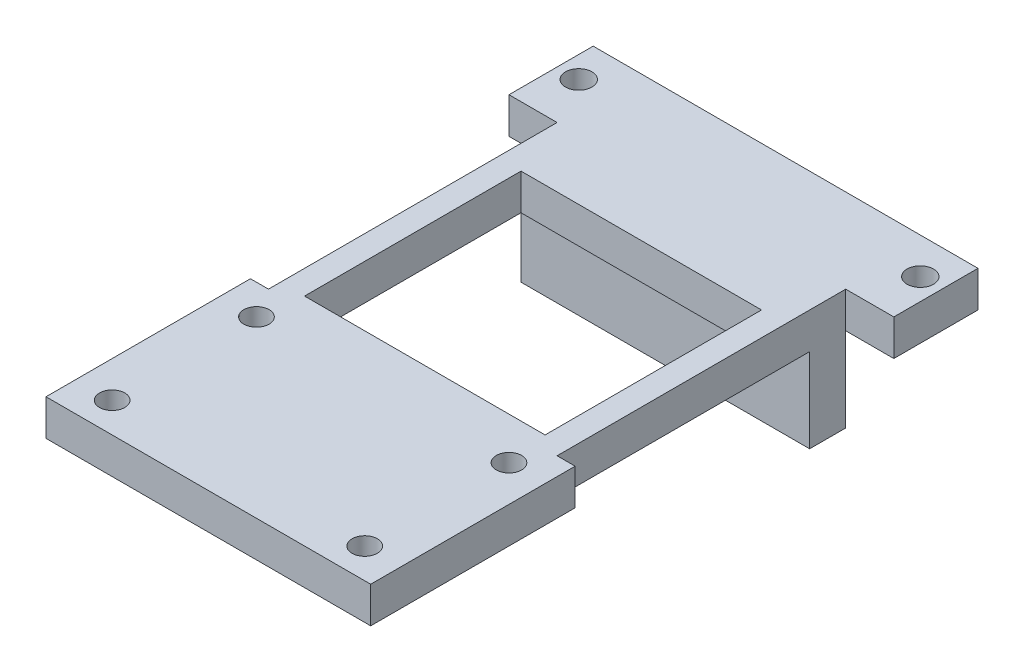
SolidWorks part; units mm, degrees
ref_plane "前视基准面" through (0, 0, 0) normal (0, 0, 1) x (1, 0, 0)
ref_plane "上视基准面" through (0, 0, 0) normal (0, 1, 0) x (1, 0, 0)
ref_plane "右视基准面" through (0, 0, 0) normal (1, 0, 0) x (0, 0, -1)
sketch "草图1" plane through (0, 0, 0) normal (0, 0, 1) x (1, 0, 0)
  line L1 (0, 0) -> (20, 0)
  line L2 (0, 0) -> (0, 10)
  line L3 (0, 10) -> (20, 10)
  line L4 (20, 0) -> (20, 10)
  dimension "D1" = 10
  dimension "D2" = 20
extrude "凸台-拉伸1" add sketch "草图1" along normal blind 3
sketch "草图2" plane through (0, 0, 3) normal (0, 0, 1) x (1, 0, 0)
  line L0 (20, 0) -> (20, 10) construction
  line L1 (0, 10) -> (20, 10)
  line L2 (0, 10) -> (0, 7)
  line L3 (0, 7) -> (20, 7)
  line L4 (20, 10) -> (20, 7)
  dimension "D1" = 3
extrude "凸台-拉伸2" add sketch "草图2" along normal blind 18
sketch "草图3" plane through (0, 7, 0) normal (0, -1, 0) x (1, 0, 0)
  line L0 (0, 3) -> (20, 3) construction
  line L1 (2, 18) -> (18, 18)
  line L2 (2, 18) -> (2, 6)
  line L3 (2, 6) -> (18, 6)
  line L4 (18, 18) -> (18, 6)
  line L6 (0, 21) -> (0, 3) construction
  line L7 (20, 21) -> (20, 3) construction
  dimension "D1" = 3
  dimension "D2" = 12
  dimension "D3" = 2
  dimension "D4" = 2
extrude "切除-拉伸1" cut sketch "草图3" against normal blind 8
sketch "草图4" plane through (0, 7, 0) normal (0, -1, 0) x (1, 0, 0)
  line L0 (0, 21) -> (-3.5, 21)
  line L1 (-3.5, 21) -> (-3.5, 38)
  line L2 (-3.5, 38) -> (23.5, 38)
  line L3 (23.5, 38) -> (23.5, 21)
  line L4 (23.5, 21) -> (0, 21)
  line L5 (0, 21) -> (0, 3) construction
  dimension "D1" = 27
  dimension "D2" = 3.5
  dimension "D3" = 17
extrude "凸台-拉伸3" add sketch "草图4" against normal blind 3
sketch "草图5" plane through (0, 7, 0) normal (0, -1, 0) x (1, 0, 0)
  line L0 (-3.5, 38) -> (-3.5, 21) construction
  line L1 (23.5, 21) -> (23.5, 38) construction
  line L2 (-3.5, 21) -> (0, 21) construction
  circle A0 centre (-0.5, 23.5) radius 1.05
  circle A1 centre (20.5, 23.5) radius 1.05
  circle A2 centre (20.5, 35.5) radius 1.05
  circle A3 centre (-0.5, 35.5) radius 1.05
  dimension "D1" = 2.1
  dimension "D2" = 2.1
  dimension "D3" = 2.1
  dimension "D4" = 2.1
  dimension "D5" = 21
  dimension "D6" = 3
  dimension "D7" = 3
  dimension "D8" = 21
  dimension "D9" = 3
  dimension "D10" = 3
  dimension "D11" = 12
  dimension "D12" = 2.5
extrude "切除-拉伸2" cut sketch "草图5" against normal blind 10
fillet "圆角2" radius 1 1 edges at (10, 0, 3)
fillet "圆角3" radius 1 6 edges at (20, 0, 1) (20, 0.2929, 2.7071) (0, 0, 1) (0, 0.2929, 2.7071) (20, 4, 3) (0, 4, 3)
fillet "圆角4" radius 1 4 edges at (10, 7, 6) (2, 7, 12) (18, 7, 12) (10, 7, 18)
sketch "草图6" plane through (0, 10, 0) normal (0, 1, 0) x (1, 0, 0)
  line L0 (0, -21) -> (0, 0)
  line L1 (0, 0) -> (20, 0)
  line L2 (20, 0) -> (20, -21)
  line L3 (20, -21) -> (0, -21)
extrude "切除-拉伸3" cut sketch "草图6" against normal blind 10
sketch "草图7" plane through (0, 10, 0) normal (0, 1, 0) x (1, 0, 0)
  line L0 (22, -21) -> (22, 3)
  line L1 (-3.5, -21) -> (23.5, -21) construction
  line L2 (22, 3) -> (-2, 3)
  line L3 (-2, 3) -> (-2, -21)
  line L4 (22, -21) -> (-2, -21)
  line L5 (23.5, -21) -> (23.5, -38) construction
  dimension "D1" = 24
  dimension "D2" = 1.5
  dimension "D3" = 24
extrude "凸台-拉伸4" add sketch "草图7" against normal blind 3
sketch "草图8" plane through (0, 7, 0) normal (0, -1, 0) x (1, 0, 0)
  line L0 (22, 21) -> (22, -3) construction
  line L1 (-2, -3) -> (22, -3)
  line L2 (-2, -3) -> (-2, 0)
  line L3 (-2, 0) -> (22, 0)
  line L4 (22, -3) -> (22, 0)
  dimension "D1" = 3
extrude "凸台-拉伸5" add sketch "草图8" along normal blind 7
sketch "草图9" plane through (0, 10, 0) normal (0, 1, 0) x (1, 0, 0)
  line L10 (22, 3) -> (-2, 3) construction
  line L11 (20, -20) -> (0, -20)
  line L12 (20, -20) -> (20, -2)
  line L13 (20, -2) -> (0, -2)
  line L14 (0, -20) -> (0, -2)
  line L15 (22, -21) -> (22, 3) construction
  line L16 (-2, 3) -> (-2, -21) construction
  dimension "D1" = 5
  dimension "D2" = 2
  dimension "D3" = 2
  dimension "D4" = 18
extrude "切除-拉伸4" cut sketch "草图9" against normal blind 7
sketch "草图10" plane through (0, 10, 0) normal (0, 1, 0) x (1, 0, 0)
  line L0 (22, -21) -> (22, 3) construction
  line L1 (-6, 3) -> (26, 3)
  line L2 (-6, 3) -> (-6, 10)
  line L3 (-6, 10) -> (26, 10)
  line L4 (26, 3) -> (26, 10)
  line L6 (22, 3) -> (-2, 3) construction
  dimension "D1" = 32
  dimension "D2" = 4
  dimension "D3" = 7
  dimension "D4" = 0
extrude "凸台-拉伸6" add sketch "草图10" against normal blind 3
sketch "草图11" plane through (0, 10, 0) normal (0, 1, 0) x (1, 0, 0)
  line L0 (26, 3) -> (26, 10) construction
  line L1 (-6, 10) -> (-6, 3) construction
  line L2 (22, 3) -> (26, 3) construction
  circle A0 centre (-4.2, 7) radius 1.1
  circle A1 centre (24.2, 7) radius 1.1
  point P6 (26, 6.5)
  dimension "D1" = 2.2
  dimension "D2" = 2.2
  dimension "D3" = 1.8
  dimension "D4" = 1.8
  dimension "D5" = 28.4
  dimension "D6" = 4
extrude "切除-拉伸5" cut sketch "草图11" against normal blind 4
